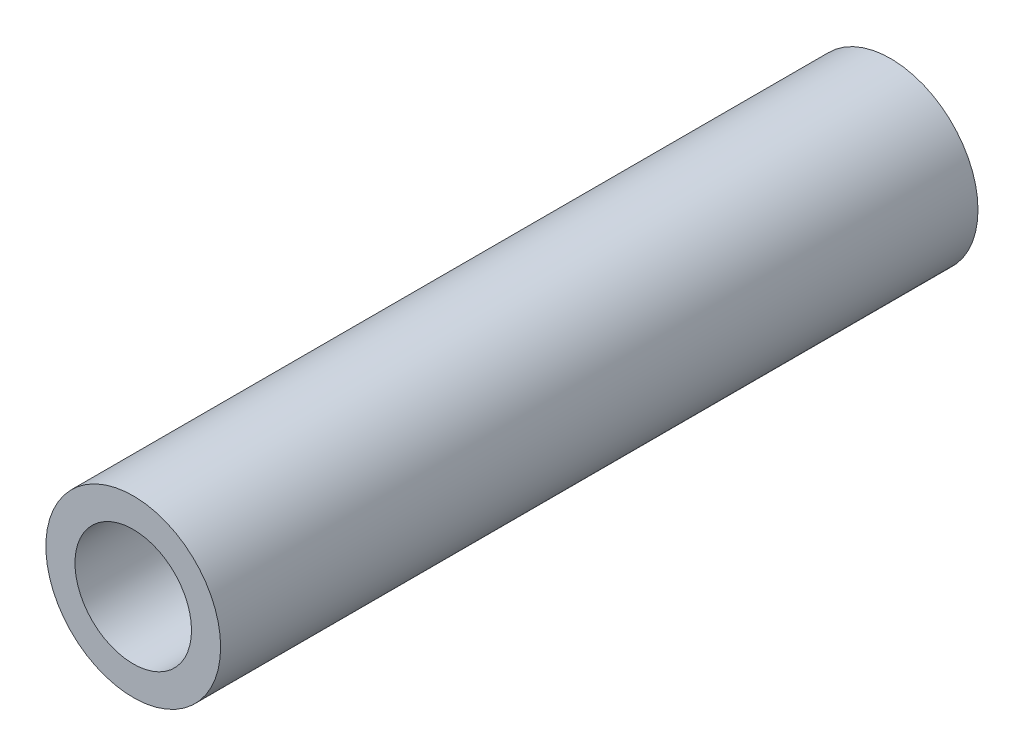
SolidWorks part; units mm, degrees
ref_plane "Front Plane" through (0, 0, 0) normal (0, 0, 1) x (1, 0, 0)
ref_plane "Top Plane" through (0, 0, 0) normal (0, 1, 0) x (1, 0, 0)
ref_plane "Right Plane" through (0, 0, 0) normal (1, 0, 0) x (0, 0, -1)
sketch "Sketch1" plane through (0, 0, 0) normal (0, 0, 1) x (1, 0, 0)
  circle A0 centre (0, 0) radius 1.5
  circle A1 centre (0, 0) radius 1
  dimension "D1" = 2
  dimension "D2" = 3
extrude "Boss-Extrude1" add sketch "Sketch1" along normal blind 13
